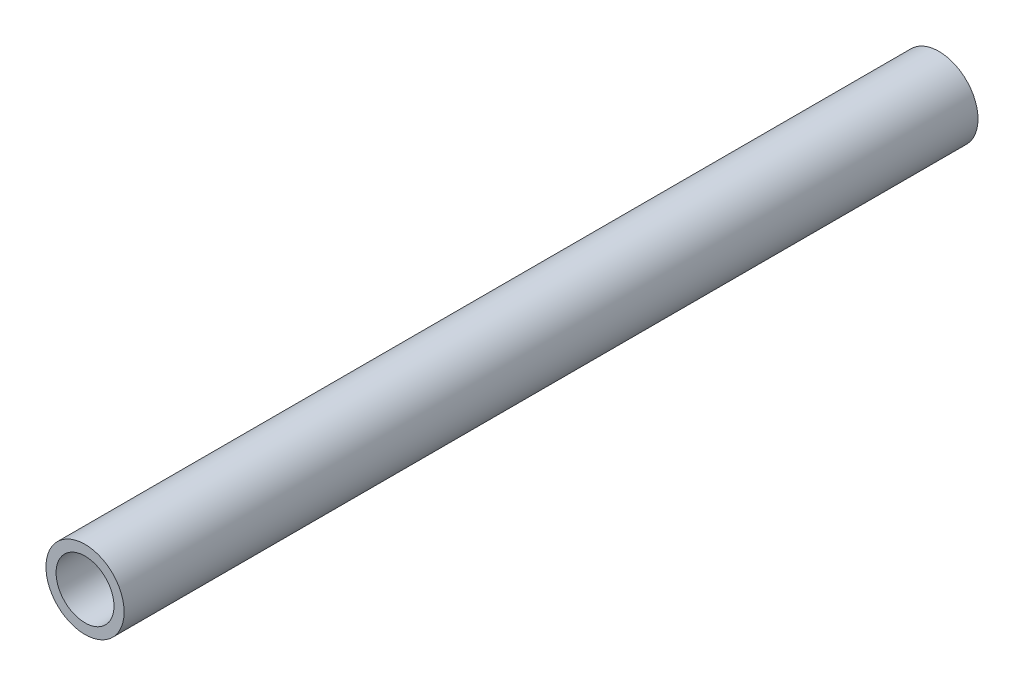
SolidWorks part; units mm, degrees
ref_plane "Front Plane" through (0, 0, 0) normal (0, 0, 1) x (1, 0, 0)
ref_plane "Top Plane" through (0, 0, 0) normal (0, 1, 0) x (1, 0, 0)
ref_plane "Right Plane" through (0, 0, 0) normal (1, 0, 0) x (0, 0, -1)
sketch "Sketch1" plane through (0, 0, 0) normal (0, 0, 1) x (1, 0, 0)
  circle A0 centre (0, 0) radius 10.668
  dimension "Pipe OD" = 21.336
extrude "Extrude-Thin1" add sketch "Sketch1" along normal blind 141.5 and the other way blind 91.5 thin thin type one direction reverse wall 2.7686
